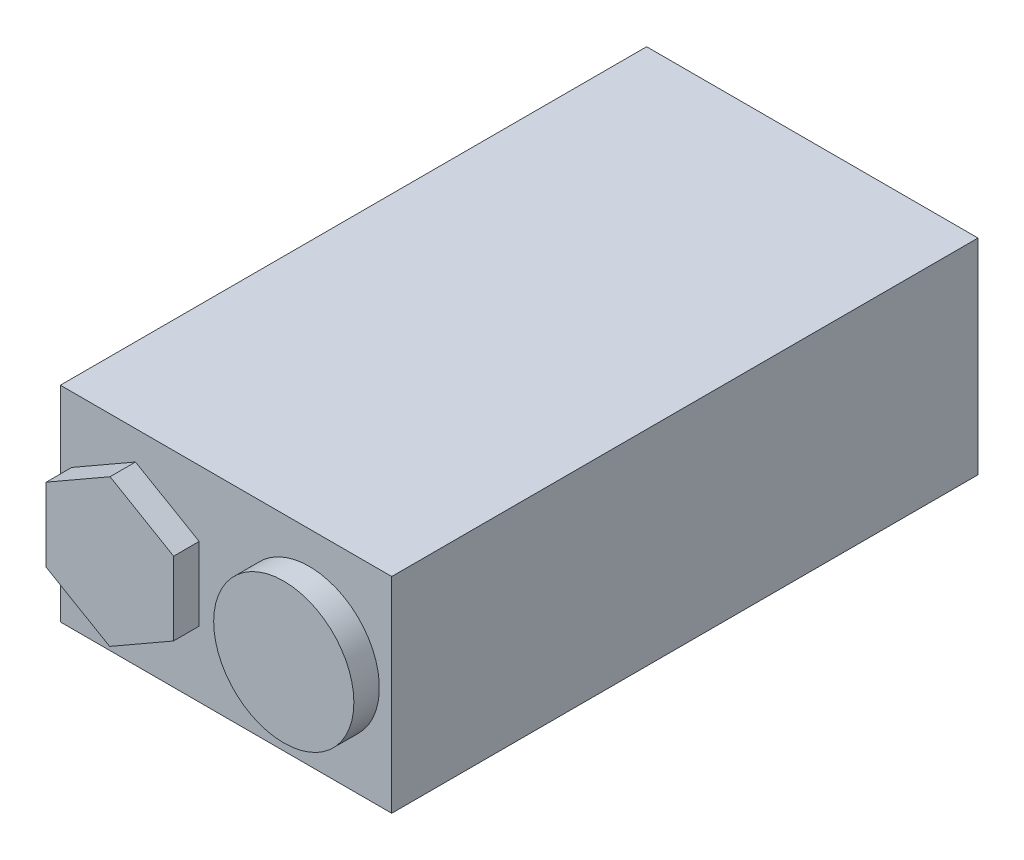
SolidWorks part; units mm, degrees
ref_plane "Front Plane" through (0, 0, 0) normal (0, 0, 1) x (1, 0, 0)
ref_plane "Top Plane" through (0, 0, 0) normal (0, 1, 0) x (1, 0, 0)
ref_plane "Right Plane" through (0, 0, 0) normal (1, 0, 0) x (0, 0, -1)
sketch "Sketch1" plane through (0, 0, 0) normal (0, 0, 1) x (1, 0, 0)
  line L1 (13, 8.045) -> (-13, 8.045)
  line L2 (13, 8.045) -> (13, -8.045)
  line L3 (13, -8.045) -> (-13, -8.045)
  line L4 (-13, 8.045) -> (-13, -8.045)
  line L5 (13, 8.045) -> (-13, -8.045) construction
  line L6 (13, -8.045) -> (-13, 8.045) construction
  point P0 (0, 0)
  dimension "D1" = 26
  dimension "D2" = 16.09
extrude "Boss-Extrude1" add sketch "Sketch1" along normal blind 46
sketch "Sketch2" plane through (0, 0, 46) normal (0, 0, 1) x (1, 0, 0)
  line L1 (-7.1348, -5.7735) -> (-2.1269, -2.9003)
  line L2 (-2.1269, -2.9003) -> (-2.1113, 2.8732)
  line L3 (-2.1113, 2.8732) -> (-7.1034, 5.7735)
  line L4 (-7.1034, 5.7735) -> (-12.1112, 2.9003)
  line L5 (-12.1112, 2.9003) -> (-12.1269, -2.8732)
  line L6 (-12.1269, -2.8732) -> (-7.1348, -5.7735)
  circle A0 centre (-7.1191, 0) radius 5 construction
  circle A1 centre (6.5294, 0) radius 5.5
  point P10 (0, 0)
  point P12 (-7.121, 0)
  point P13 (-7.1191, 5.2769)
  point P14 (6.5294, 0)
  dimension "D1" = 10
  dimension "D2" = 11
extrude "Boss-Extrude2" add sketch "Sketch2" along normal blind 2
